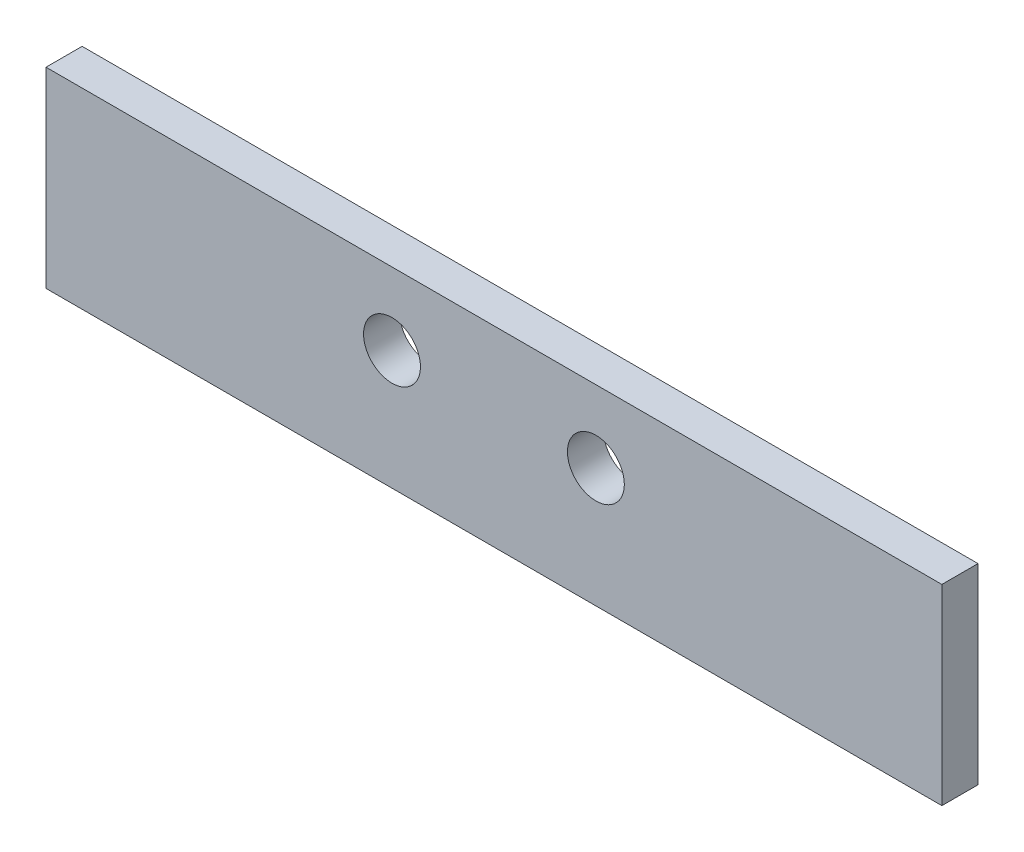
SolidWorks part; units mm, degrees
material "Silicon Rubber"
ref_plane "Front Plane" through (0, 0, 0) normal (0, 0, 1) x (1, 0, 0)
ref_plane "Top Plane" through (0, 0, 0) normal (0, 1, 0) x (1, 0, 0)
ref_plane "Right Plane" through (0, 0, 0) normal (1, 0, 0) x (0, 0, -1)
sketch "Sketch1" plane through (0, 0, 0) normal (0, 0, 1) x (1, 0, 0)
  line L1 (-39.37, -8.4201) -> (39.37, -8.4201)
  line L2 (-39.37, -8.4201) -> (-39.37, 8.4201)
  line L3 (-39.37, 8.4201) -> (39.37, 8.4201)
  line L4 (39.37, -8.4201) -> (39.37, 8.4201)
  line L5 (-39.37, -8.4201) -> (39.37, 8.4201) construction
  line L6 (-39.37, 8.4201) -> (39.37, -8.4201) construction
  point P0 (0, 0)
  dimension "D1" = 78.74
  dimension "D2" = 16.8402
extrude "Boss-Extrude1" add sketch "Sketch1" along normal blind 3.175
sketch "Sketch2" plane through (0, 0, 3.175) normal (0, 0, 1) x (1, 0, 0)
  line L0 (0, 8.4201) -> (0, -4.2799) construction
  line L1 (39.37, 8.4201) -> (-39.37, 8.4201) construction
  line L2 (0, -4.2799) -> (39.37, -4.2799) construction
  line L3 (39.37, -8.4201) -> (39.37, 8.4201) construction
  line L4 (0, 2.0701) -> (39.37, 2.0701) construction
  line L5 (0, 2.0701) -> (-39.37, 2.0701) construction
  line L6 (-39.37, 8.4201) -> (-39.37, -8.4201) construction
  line L7 (-8.9598, -0.4299) -> (8.9598, -0.4299) construction
  circle A0 centre (-8.9598, 2.0701) radius 2.5
  circle A1 centre (8.9598, 2.0701) radius 2.5
  point P19 (0, -0.4299)
  dimension "D2" = 5
  dimension "D3" = 17.9197
  dimension "D1" = 12.7
extrude "Cut-Extrude1" cut sketch "Sketch2" against normal through all
